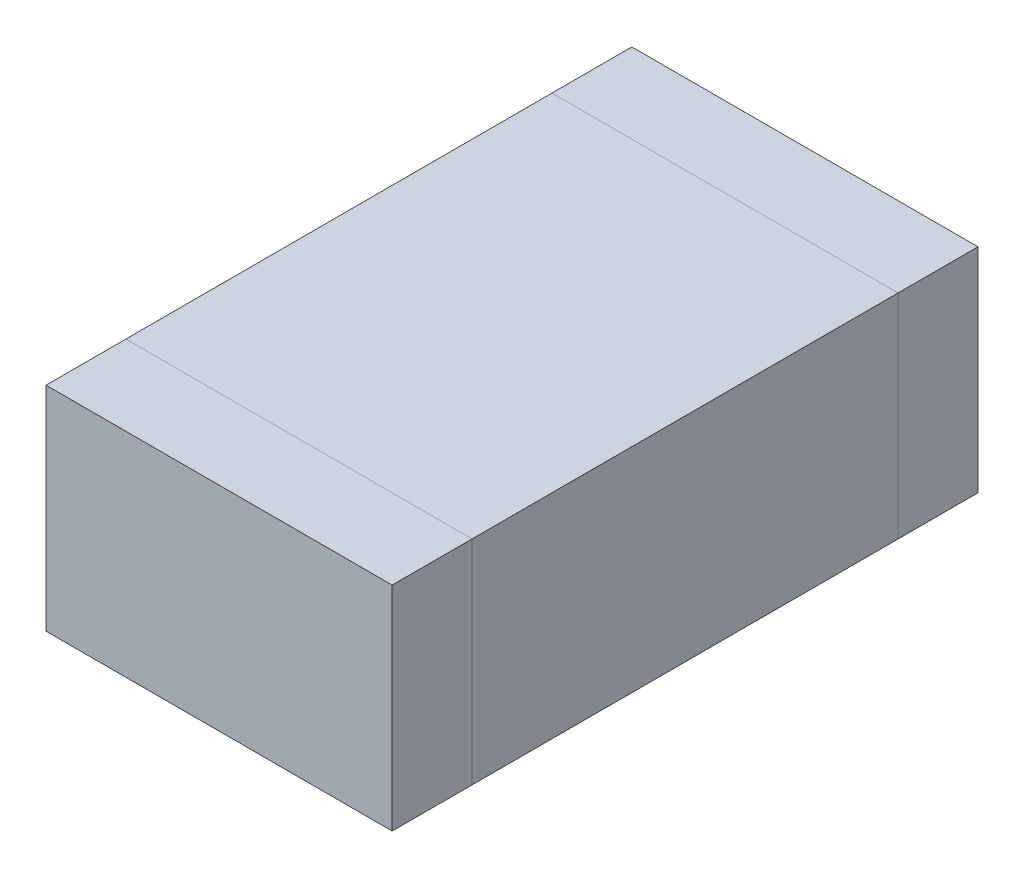
SolidWorks part; units mm, degrees
ref_plane "Front Plane" through (0, 0, 0) normal (0, 0, 1) x (1, 0, 0)
ref_plane "Top Plane" through (0, 0, 0) normal (0, 1, 0) x (1, 0, 0)
ref_plane "Right Plane" through (0, 0, 0) normal (1, 0, 0) x (0, 0, -1)
sketch "Sketch1" plane through (0, 0, 0) normal (0, 1, 0) x (1, 0, 0)
  line L1 (-0.65, 0.8) -> (0.65, 0.8)
  line L2 (-0.65, 0.8) -> (-0.65, -0.8)
  line L3 (-0.65, -0.8) -> (0.65, -0.8)
  line L4 (0.65, 0.8) -> (0.65, -0.8)
  line L5 (-0.65, 0.8) -> (0.65, -0.8) construction
  line L6 (-0.65, -0.8) -> (0.65, 0.8) construction
  point P0 (0, 0)
  dimension "Length" = 1.6
  dimension "Width" = 1.3
extrude "MB" add sketch "Sketch1" along normal blind 0.8
sketch "Sketch2" plane through (0, 0, 0.8) normal (0, 0, 1) x (1, 0, 0)
  line L4 (-0.65, 0) -> (0.65, 0)
  line L5 (0.65, 0) -> (0.65, 0.8)
  line L6 (0.65, 0.8) -> (-0.65, 0.8)
  line L7 (-0.65, 0.8) -> (-0.65, 0)
  line L8 (-0.65, 0) -> (0.65, 0)
  line L9 (0.65, 0) -> (0.65, 0.8)
  line L10 (0.65, 0.8) -> (-0.65, 0.8)
  line L11 (-0.65, 0.8) -> (-0.65, 0)
  dimension "D1" = 0
extrude "SB L" add sketch "Sketch2" along normal blind 0.3 separate body
sketch "Sketch3" plane through (0, 0, -0.8) normal (0, 0, -1) x (-1, 0, 0)
  line L4 (-0.65, 0) -> (0.65, 0)
  line L5 (0.65, 0) -> (0.65, 0.8)
  line L6 (0.65, 0.8) -> (-0.65, 0.8)
  line L7 (-0.65, 0.8) -> (-0.65, 0)
  line L8 (-0.65, 0) -> (0.65, 0)
  line L9 (0.65, 0) -> (0.65, 0.8)
  line L10 (0.65, 0.8) -> (-0.65, 0.8)
  line L11 (-0.65, 0.8) -> (-0.65, 0)
  dimension "D1" = 0
extrude "SB R" add sketch "Sketch3" along normal blind 0.3 separate body
